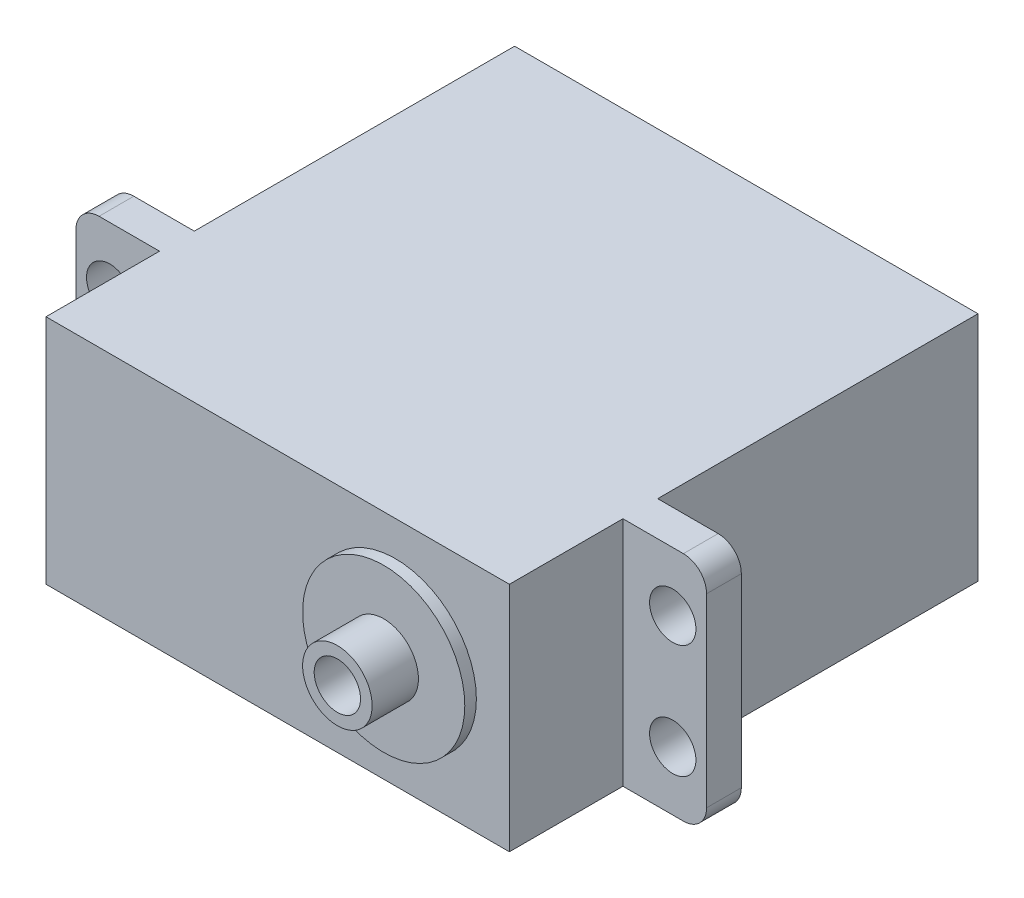
SolidWorks part; units mm, degrees
ref_plane "Front Plane" through (0, 0, 0) normal (0, 0, 1) x (1, 0, 0)
ref_plane "Top Plane" through (0, 0, 0) normal (0, 1, 0) x (1, 0, 0)
ref_plane "Right Plane" through (0, 0, 0) normal (1, 0, 0) x (0, 0, -1)
sketch "Sketch2" plane through (0, 0, 0) normal (0, 0, 1) x (1, 0, 0)
  line L1 (-13.5922, 208.3879) -> (-53.5922, 208.3879)
  line L2 (-13.5922, 208.3879) -> (-13.5922, 228.3879)
  line L3 (-13.5922, 228.3879) -> (-53.5922, 228.3879)
  line L4 (-53.5922, 208.3879) -> (-53.5922, 228.3879)
  dimension "D1" = 40
  dimension "D2" = 20
extrude "Boss-Extrude1" add sketch "Sketch2" along normal blind 27.65
sketch "Sketch3" plane through (0, 0, 27.65) normal (0, 0, 1) x (1, 0, 0)
  line L0 (-53.5922, 208.3879) -> (-13.5922, 208.3879) construction
  line L1 (-6.3722, 208.3879) -> (-60.8122, 208.3879)
  line L2 (-6.3722, 208.3879) -> (-6.3722, 228.3879)
  line L3 (-6.3722, 228.3879) -> (-60.8122, 228.3879)
  line L4 (-60.8122, 208.3879) -> (-60.8122, 228.3879)
  line L5 (-13.5922, 228.3879) -> (-53.5922, 228.3879) construction
  line L6 (-13.5922, 218.3879) -> (-53.5922, 218.3879) construction
  line L7 (-13.5922, 208.3879) -> (-13.5922, 228.3879) construction
  line L8 (-53.5922, 228.3879) -> (-53.5922, 208.3879) construction
  line L9 (-33.5922, 218.3879) -> (-33.5922, 214.2288) construction
  circle A0 centre (-9.2922, 213.4879) radius 2
  circle A1 centre (-9.2922, 223.2879) radius 2
  circle A2 centre (-57.8922, 223.2879) radius 2
  circle A3 centre (-57.8922, 213.4879) radius 2
  dimension "D1" = 0
  dimension "D2" = 0
  dimension "D3" = 54.44
  dimension "D4" = 27.22
extrude "Boss-Extrude2" add sketch "Sketch3" along normal blind 3
sketch "Sketch4" plane through (0, 0, 30.65) normal (0, 0, 1) x (1, 0, 0)
  line L4 (-13.5922, 208.3879) -> (-13.5922, 228.3879)
  line L5 (-53.5922, 208.3879) -> (-13.5922, 208.3879)
  line L6 (-53.5922, 228.3879) -> (-53.5922, 208.3879)
  line L7 (-13.5922, 228.3879) -> (-53.5922, 228.3879)
  line L8 (-13.5922, 208.3879) -> (-13.5922, 228.3879)
  line L9 (-53.5922, 208.3879) -> (-13.5922, 208.3879)
  line L10 (-53.5922, 228.3879) -> (-53.5922, 208.3879)
  line L11 (-13.5922, 228.3879) -> (-53.5922, 228.3879)
  dimension "D1" = 0
extrude "Boss-Extrude3" add sketch "Sketch4" along normal blind 9.8
sketch "Sketch5" plane through (0, 0, 40.45) normal (0, 0, 1) x (1, 0, 0)
  circle A0 centre (-23.4422, 218.3879) radius 7
  circle A1 centre (-57.8922, 223.2879) radius 2 construction
  dimension "D1" = 34.45
extrude "Boss-Extrude4" add sketch "Sketch5" along normal blind 1
sketch "Sketch6" plane through (0, 0, 41.45) normal (0, 0, 1) x (1, 0, 0)
  circle A0 centre (-23.4422, 218.3879) radius 3
extrude "Boss-Extrude5" add sketch "Sketch6" along normal blind 4
fillet "Fillet1" radius 2
sketch "Sketch7" plane through (0, 0, 45.45) normal (0, 0, 1) x (1, 0, 0)
  circle A2 centre (-23.4422, 218.3879) radius 2
  circle A3 centre (-23.4422, 218.3879) radius 2
  dimension "D1" = 1
extrude "Cut-Extrude1" cut sketch "Sketch7" against normal blind 10
